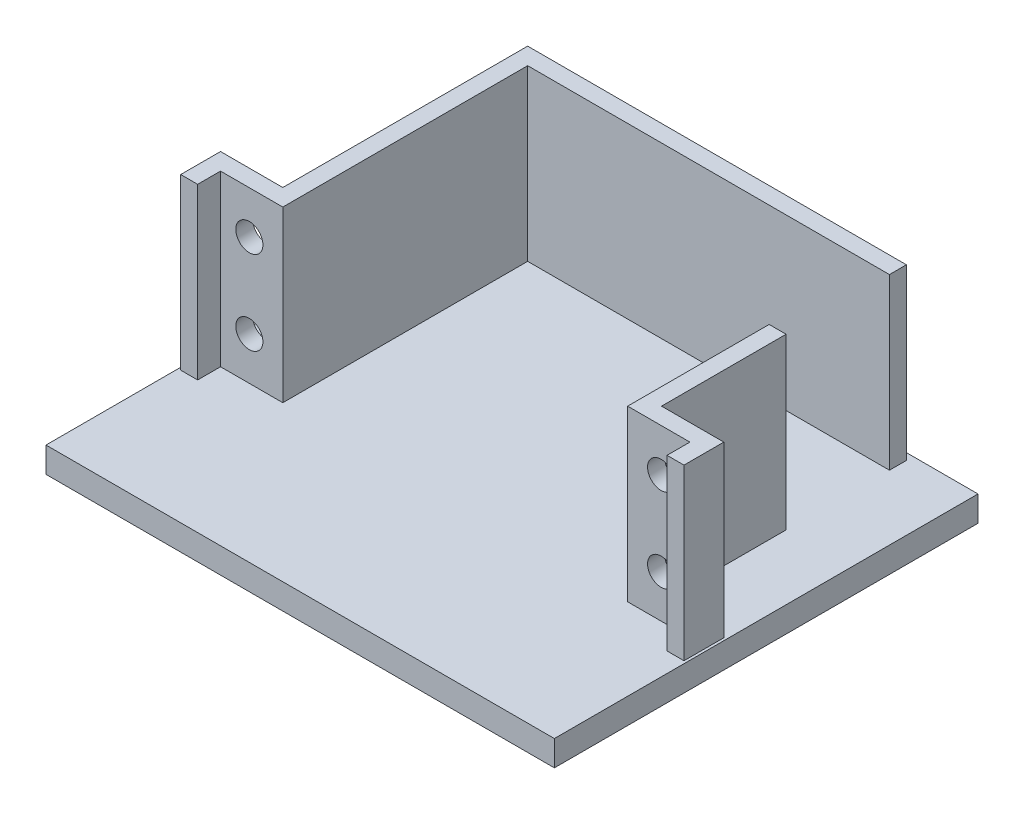
SolidWorks part; units mm, degrees
ref_plane "Front Plane" through (0, 0, 0) normal (0, 0, 1) x (1, 0, 0)
ref_plane "Top Plane" through (0, 0, 0) normal (0, 1, 0) x (1, 0, 0)
ref_plane "Right Plane" through (0, 0, 0) normal (1, 0, 0) x (0, 0, -1)
sketch "Sketch1" plane through (0, 0, 0) normal (0, 1, 0) x (1, 0, 0)
  line L2 (-20.35, 22.2) -> (22.35, 22.2)
  line L7 (20.35, -6.7) -> (20.35, 10)
  line L8 (-20.35, -6.7) -> (-27.7, -6.7)
  line L9 (-20.35, 22.2) -> (-20.35, -6.7)
  line L10 (20.35, -6.7) -> (27.7, -6.7)
  line L11 (-27.7, -6.7) -> (-27.7, -9.4)
  line L12 (27.7, -6.7) -> (27.7, -9.4)
  line L13 (-29.7, -4.7) -> (-29.7, -9.4)
  line L14 (-22.35, -4.7) -> (-29.7, -4.7)
  line L15 (-22.35, 24.2) -> (-22.35, -4.7)
  line L16 (-22.35, 24.2) -> (22.35, 24.2)
  line L17 (29.7, -4.7) -> (29.7, -9.4)
  line L18 (22.35, -4.7) -> (29.7, -4.7)
  line L19 (22.35, -4.7) -> (22.35, 10)
  line L20 (-29.7, -9.4) -> (-27.7, -9.4)
  line L21 (27.7, -9.4) -> (29.7, -9.4)
  line L22 (20.35, 10) -> (22.35, 10)
  line L23 (-20.35, 22.2) -> (20.3495, 22.2) construction
  line L24 (-22.35, 24.2) -> (20.3495, 24.2) construction
  line L25 (22.35, 24.2) -> (22.35, 22.2)
  point P4 (0, 0)
  point P8 (0, 0)
  point P17 (0, 22.5)
extrude "Boss-Extrude2" add sketch "Sketch1" along normal blind 20
sketch "Sketch3" plane through (0, 0, 0) normal (0, 1, 0) x (1, 0, 0)
  line L2 (-30, 25) -> (30, 25)
  line L3 (-30, 25) -> (-30, -25)
  line L4 (-30, -25) -> (30, -25)
  line L5 (30, 25) -> (30, -25)
  point P3 (0, 0)
  point P6 (0, 0)
extrude "Boss-Extrude3" add sketch "Sketch3" against normal blind 3
sketch "Sketch4" plane through (0, 0, 0) normal (0, 0, 1) x (1, 0, 0)
  circle A0 centre (-24.3, 14.95) radius 1.6
  circle A1 centre (24.3, 14.95) radius 1.6
  circle A2 centre (24.3, 5.05) radius 1.6
  circle A3 centre (-24.3, 5.05) radius 1.6
  point P8 (0, 10)
extrude "Cut-Extrude1" cut sketch "Sketch4" along normal blind 10
